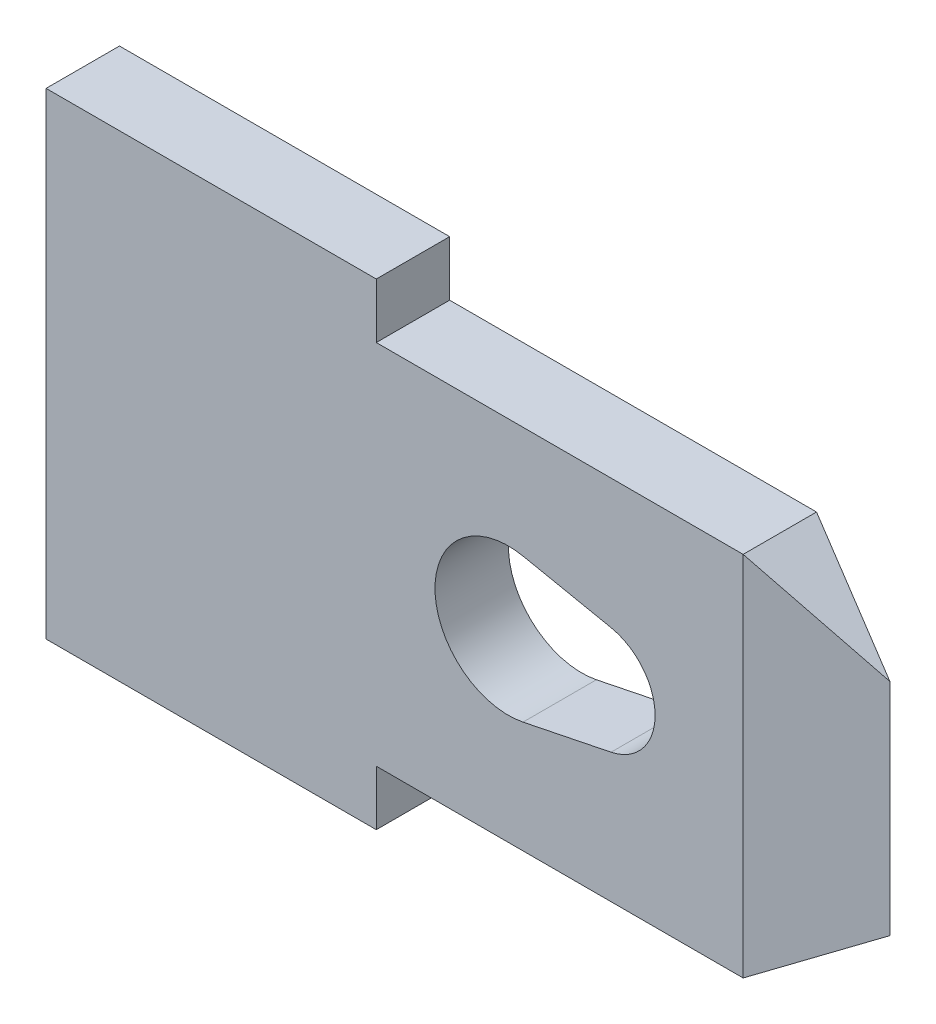
SolidWorks part; units mm, degrees
material "1.4301 (X5CrNi18-10)"
ref_plane "Płaszczyzna przednia" through (0, 0, 0) normal (0, 0, 1) x (1, 0, 0)
ref_plane "Płaszczyzna górna" through (0, 0, 0) normal (0, 1, 0) x (1, 0, 0)
ref_plane "Płaszczyzna prawa" through (0, 0, 0) normal (1, 0, 0) x (0, 0, -1)
sketch "Szkic1" plane through (0, 0, 0) normal (0, 0, 1) x (1, 0, 0)
  line L0 (0, 0) -> (11, 0) construction
  line L1 (0, -3.25) -> (0, 3.25)
  line L2 (0, 3.25) -> (4.5, 3.25)
  line L3 (4.5, 3.25) -> (4.5, 2.5)
  line L4 (4.5, 2.5) -> (9.5, 2.5)
  line L5 (9.5, 2.5) -> (11, 1.5)
  line L6 (11, 1.5) -> (11, -1.5)
  line L7 (9.5, -2.5) -> (11, -1.5)
  line L8 (4.5, -2.5) -> (9.5, -2.5)
  line L9 (4.5, -3.25) -> (4.5, -2.5)
  line L10 (0, -3.25) -> (4.5, -3.25)
  dimension "D1" = 11
  dimension "D2" = 6.5
  dimension "D3" = 5
  dimension "D4" = 3
  dimension "D5" = 4.5
  dimension "D6" = 5
extrude "Dodanie-wyciągnięcie1" add sketch "Szkic1" along normal blind 1
sketch "Szkic2" plane through (0, 0, 1) normal (0, 0, 1) x (1, 0, 0)
  line L0 (0, 0) -> (11, 0) construction
  line L1 (0, 3.25) -> (0, -3.25) construction
  line L2 (11, -1.5) -> (11, 1.5) construction
  line L3 (6.5, 0.9798) -> (7.7, 0.7348)
  line L4 (6.5, -0.9798) -> (7.7, -0.7348)
  arc A0 (6.5, 0.9798) -> (6.5, -0.9798) centre (6.3, 0) ccw
  arc A1 (7.7, -0.7348) -> (7.7, 0.7348) centre (7.55, 0) ccw
  dimension "D1" = 2
  dimension "D2" = 1.5
  dimension "D3" = 1.25
  dimension "D4" = 3.45
extrude "Wytnij-wyciągnięcie1" cut sketch "Szkic2" against normal up to next
sketch "Szkic3" plane through (0, 2.5, 0) normal (0, 1, 0) x (1, 0, 0)
  line L0 (11, -0.5) -> (9.5, 0)
  line L1 (11, -1) -> (11, 0) construction
  line L2 (9.5, 0) -> (9.5, -1) construction
  line L3 (9.5, -1) -> (11, -0.5)
  line L4 (9.5, 0) -> (11, 0)
  line L5 (11, 0) -> (11, -1)
  line L6 (11, -1) -> (9.5, -1)
extrude "Wytnij-wyciągnięcie2" cut sketch "Szkic3" against normal up to next contours L6 L5 L3 | L5 L4 L0
